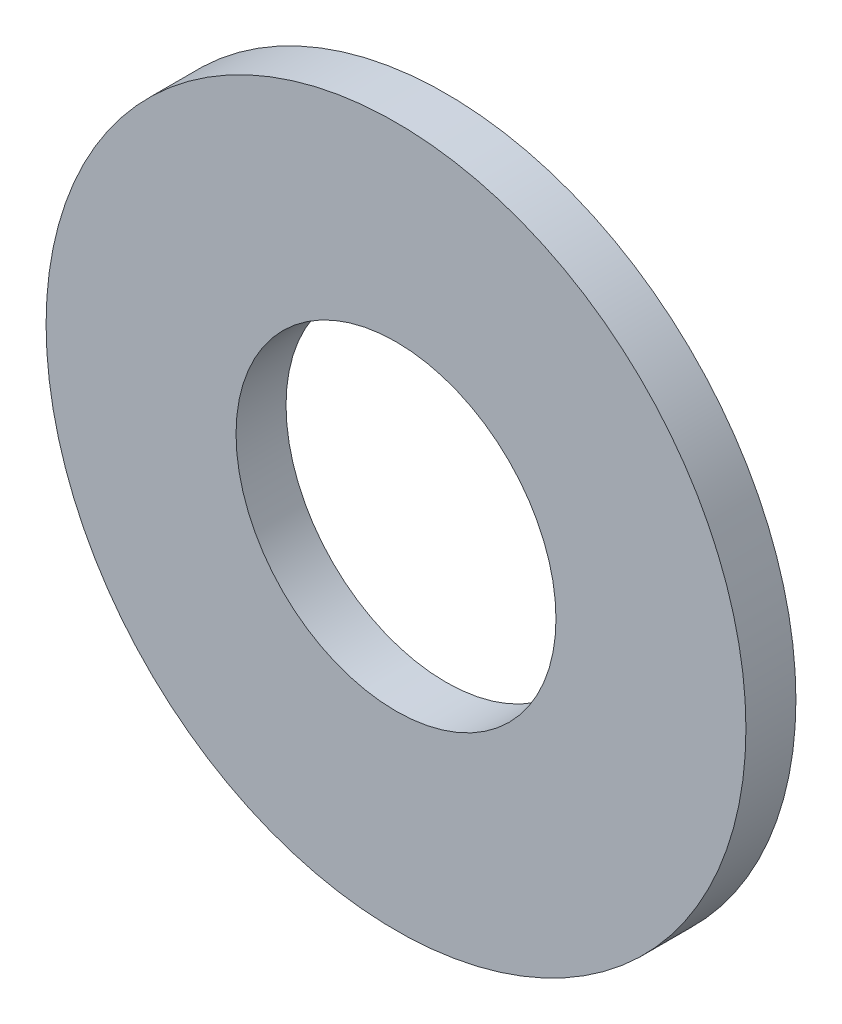
SolidWorks part; units mm, degrees
ref_plane "Спереди" through (0, 0, 0) normal (0, 0, 1) x (1, 0, 0)
ref_plane "Сверху" through (0, 0, 0) normal (0, 1, 0) x (1, 0, 0)
ref_plane "Справа" through (0, 0, 0) normal (1, 0, 0) x (0, 0, -1)
sketch "Эскиз1" plane through (0, 0, 0) normal (0, 0, 1) x (1, 0, 0)
  circle A0 centre (0, 0) radius 1.6
  circle A1 centre (0, 0) radius 3.5
extrude "Бобышка-Вытянуть1" add sketch "Эскиз1" along normal blind 0.5
